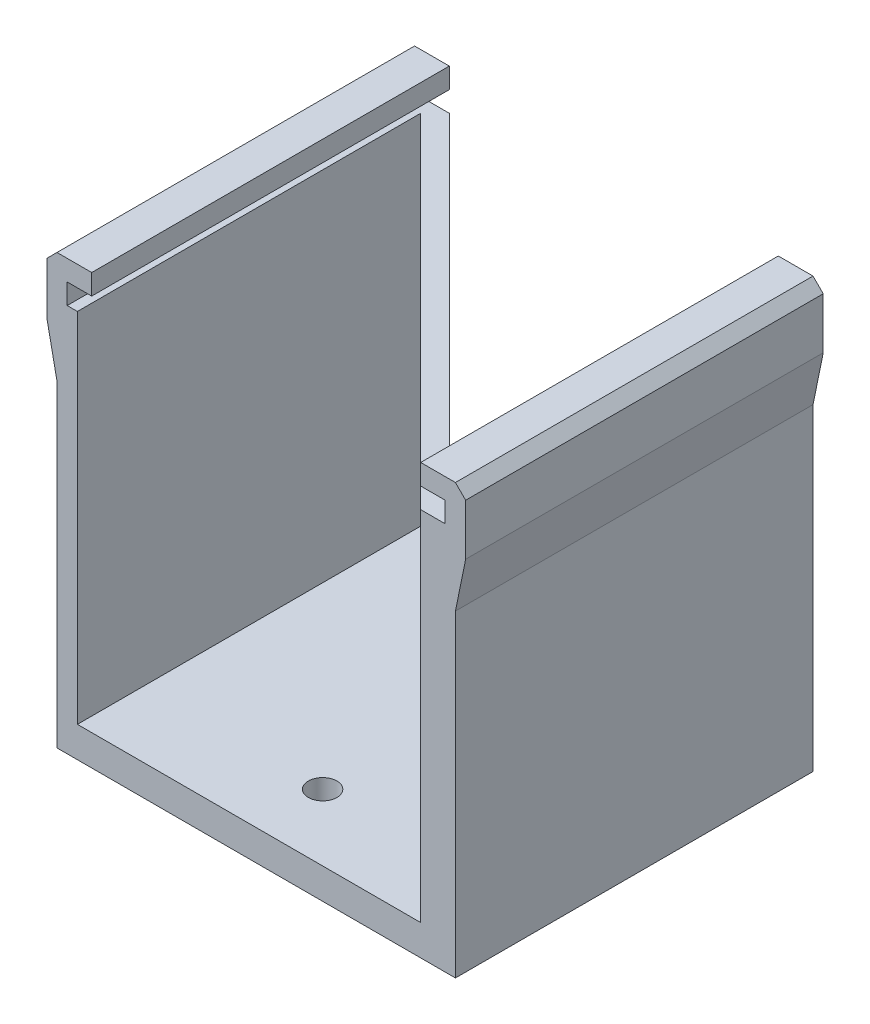
SolidWorks part; units mm, degrees
ref_plane "Front Plane" through (0, 0, 0) normal (0, 0, 1) x (1, 0, 0)
ref_plane "Top Plane" through (0, 0, 0) normal (0, 1, 0) x (1, 0, 0)
ref_plane "Right Plane" through (0, 0, 0) normal (1, 0, 0) x (0, 0, -1)
sketch "Sketch1" plane through (0, 0, 0) normal (0, 1, 0) x (1, 0, 0)
  line L1 (0, 0) -> (-35, 0)
  line L2 (0, 0) -> (0, 35)
  line L3 (0, 35) -> (-35, 35)
  line L4 (-35, 0) -> (-35, 35)
  dimension "D1" = 35
  dimension "D2" = 35
extrude "Boss-Extrude1" add sketch "Sketch1" along normal blind 3
sketch "Sketch2" plane through (0, 3, 0) normal (0, 1, 0) x (1, 0, 0)
  line L0 (-35, 33.6) -> (-1.4, 0)
  line L1 (-35, 35) -> (-35, 0) construction
  line L2 (-35, 0) -> (0, 0) construction
  line L3 (-1.4, 0) -> (0, 0)
  line L4 (0, 0) -> (0, 1.4284)
  line L5 (0, 0) -> (0, 35) construction
  line L6 (0, 1.4284) -> (-33.5716, 35)
  line L7 (0, 35) -> (-35, 35) construction
  line L8 (-33.5716, 35) -> (-35, 35)
  line L9 (-35, 35) -> (-35, 33.6)
  dimension "D1" = 45
  dimension "D2" = 45
  dimension "D3" = 2
  dimension "D4" = 1.4
extrude "Boss-Extrude2" add sketch "Sketch2" along normal blind 35
sketch "Sketch6" plane through (0, 0, 0) normal (1, 0, 0) x (0, 0, -1)
  line L1 (0, 0) -> (35, 0)
  line L2 (0, 0) -> (0, 38)
  line L3 (0, 38) -> (35, 38)
  line L4 (35, 0) -> (35, 38)
extrude "Boss-Extrude8" add sketch "Sketch6" along normal blind 2
sketch "Sketch7" plane through (-35, 0, 0) normal (-1, 0, 0) x (0, 0, 1)
  line L1 (-35, 38) -> (0, 38)
  line L2 (-35, 38) -> (-35, 0)
  line L3 (-35, 0) -> (0, 0)
  line L4 (0, 38) -> (0, 0)
extrude "Boss-Extrude9" add sketch "Sketch7" along normal blind 2
sketch "Sketch8" plane through (0, 0, 0) normal (0, -1, 0) x (1, 0, 0)
  line L0 (-37, 0) -> (2, -35) construction
  line L1 (2, -35) -> (2, 0) construction
  line L2 (2, 0) -> (-37, -35) construction
  line L3 (-37, -35) -> (-37, 0) construction
  line L4 (-17.5, 0) -> (-17.5, -35) construction
  line L5 (-37, 0) -> (2, 0) construction
  line L6 (2, -35) -> (-37, -35) construction
  circle A1 centre (-17.5, -6.5) radius 1.4
  circle A2 centre (-17.5, -28.5) radius 1.4
  point P18 (-17.5, -17.5)
  dimension "D1" = 2.8
  dimension "D2" = 2.8
  dimension "D3" = 11
  dimension "D4" = 11
extrude "Cut-Extrude1" cut sketch "Sketch8" against normal blind 10
sketch "Sketch9" plane through (0, 38, 0) normal (0, 1, 0) x (1, 0, 0)
  line L0 (-37, 0) -> (-35, 0) construction
  line L1 (-37, 35) -> (-36, 35)
  line L2 (-37, 35) -> (-37, 0)
  line L3 (-37, 0) -> (-36, 0)
  line L4 (-36, 35) -> (-36, 0)
  line L5 (2, 35) -> (0, 35) construction
  line L6 (2, 0) -> (1, 0)
  line L7 (2, 0) -> (2, 35)
  line L8 (2, 35) -> (1, 35)
  line L9 (1, 0) -> (1, 35)
extrude "Boss-Extrude10" add sketch "Sketch9" along normal blind 2
sketch "Sketch10" plane through (0, 0, 0) normal (0, 0, 1) x (1, 0, 0)
  line L1 (-37, 40) -> (-33.6, 40)
  line L2 (-37, 40) -> (-37, 42)
  line L3 (-37, 42) -> (-33.6, 42)
  line L4 (-33.6, 40) -> (-33.6, 42)
  line L5 (2, 40) -> (-1.4, 40)
  line L6 (2, 40) -> (2, 42)
  line L7 (2, 42) -> (-1.4, 42)
  line L8 (-1.4, 40) -> (-1.4, 42)
  dimension "D1" = 3.4
  dimension "D2" = 3.4
  dimension "D3" = 2
  dimension "D4" = 2
extrude "Boss-Extrude11" add sketch "Sketch10" against normal blind 35
sketch "Sketch11" plane through (0, 0, 0) normal (0, 0, 1) x (1, 0, 0)
  line L0 (-37, 42) -> (-38, 41)
  line L1 (-37, 0) -> (-37, 42) construction
  line L2 (-38, 41) -> (-38, 36)
  line L3 (-38, 36) -> (-37, 31.101)
  line L4 (-37, 42) -> (-37, 31.101)
  line L5 (2, 42) -> (3, 41)
  line L6 (2, 42) -> (2, 0) construction
  line L7 (3, 41) -> (3, 36)
  line L8 (3, 36) -> (2, 31.101)
  line L9 (2, 31.101) -> (2, 42)
  line L10 (2, 42) -> (-1.4, 42) construction
  point P10 (0, 0)
  point P13 (-38, 35.6023)
  point P15 (-38, 40.8112)
  point P16 (0, 0)
  point P19 (2, 25.5522)
  dimension "D1" = 1
  dimension "D2" = 5
  dimension "D3" = 5
  dimension "D4" = 1
  dimension "D5" = 1
  dimension "D6" = 5
  dimension "D7" = 5
  dimension "D8" = 1
extrude "Boss-Extrude12" add sketch "Sketch11" against normal blind 35
